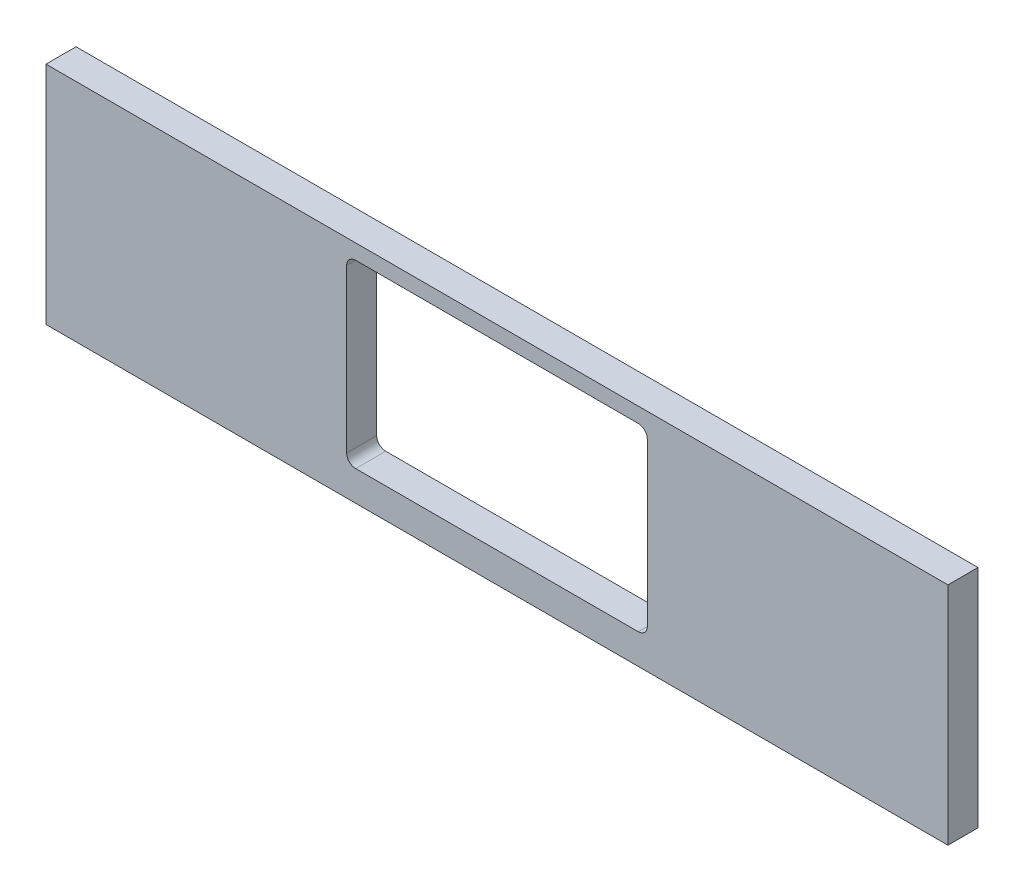
SolidWorks part; units mm, degrees
ref_plane "Ebene vorne" through (0, 0, 0) normal (0, 0, 1) x (1, 0, 0)
ref_plane "Ebene oben" through (0, 0, 0) normal (0, 1, 0) x (1, 0, 0)
ref_plane "Ebene rechts" through (0, 0, 0) normal (1, 0, 0) x (0, 0, -1)
sketch "Skizze1" plane through (0, 0, 0) normal (0, 0, 1) x (1, 0, 0)
  line L0 (-150, -75) -> (-150, 55) construction
  line L1 (150, -150) -> (-150, -150)
  line L2 (150, -150) -> (150, -75)
  line L3 (150, -75) -> (-150, -75)
  line L4 (-150, -150) -> (-150, -75)
  dimension "D1" = 75
extrude "Linear austragen1" add sketch "Skizze1" along normal blind 10
sketch "Skizze2" plane through (0, 0, 10) normal (0, 0, 1) x (1, 0, 0)
  line L0 (-150, -150) -> (150, -150) construction
  line L1 (50, -140) -> (-50, -140)
  line L2 (50, -140) -> (50, -80)
  line L3 (50, -80) -> (-50, -80)
  line L4 (-50, -140) -> (-50, -80)
  line L5 (50, -140) -> (150, -140) construction
  line L6 (150, 55) -> (150, -151) construction
  line L7 (-50, -140) -> (-150, -140) construction
  line L8 (-150, 55) -> (-150, -151) construction
  dimension "D1" = 10
  dimension "D2" = 100
  dimension "D3" = 60
extrude "Schnitt-Linear austragen1" cut sketch "Skizze2" against normal blind 10
fillet "Verrundung1" radius 3 4 edges at (-50, -140, 5) (50, -140, 5) (-50, -80, 5) (50, -80, 5)
